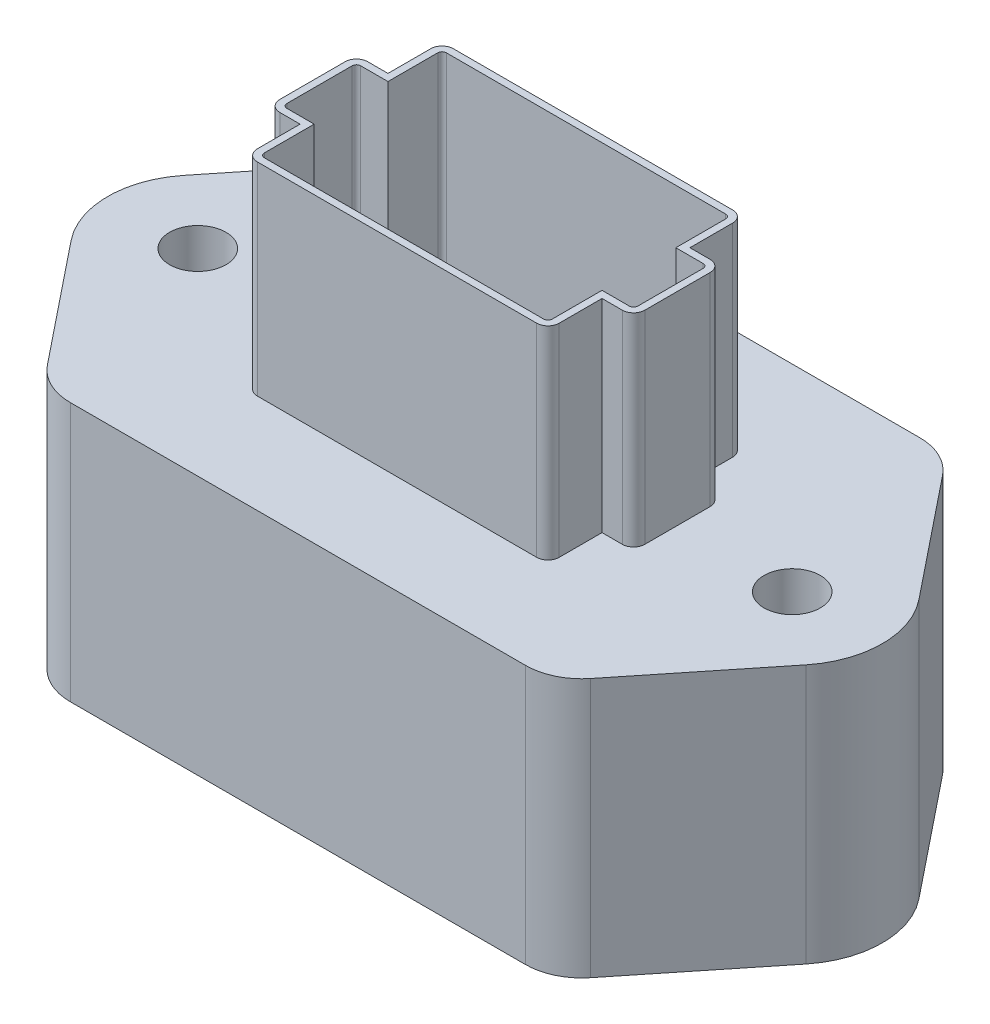
SolidWorks part; units mm, degrees
material "PA Type 6"
ref_plane "Front" through (0, 0, 0) normal (0, 0, 1) x (1, 0, 0)
ref_plane "Top" through (0, 0, 0) normal (0, 1, 0) x (1, 0, 0)
ref_plane "Right" through (0, 0, 0) normal (1, 0, 0) x (0, 0, -1)
sketch "Sketch1" plane through (0, 0, 0) normal (0, 1, 0) x (1, 0, 0)
  line L0 (30.6075, 19.848) -> (41.4283, 6.3568)
  line L1 (-25.654, -22.225) -> (25.654, -22.225)
  line L3 (-25.654, 22.225) -> (25.654, 22.225)
  line L5 (-28.7011, -22.225) -> (28.7011, 22.225) construction
  line L6 (-28.7011, 22.225) -> (28.7011, -22.225) construction
  line L7 (41.4283, -6.3568) -> (30.6075, -19.848)
  line L8 (-30.6075, -19.848) -> (-41.4283, -6.3568)
  line L9 (-41.4283, 6.3568) -> (-30.6075, 19.848)
  line L10 (-28.7011, 22.225) -> (-28.7011, -22.225) construction
  line L11 (28.7011, 22.225) -> (28.7011, -22.225) construction
  arc A0 (25.654, -22.225) -> (30.6075, -19.848) centre (25.654, -15.875) ccw
  arc A1 (-25.654, -22.225) -> (-30.6075, -19.848) centre (-25.654, -15.875) cw
  arc A2 (25.654, 22.225) -> (30.6075, 19.848) centre (25.654, 15.875) cw
  arc A3 (-30.6075, 19.848) -> (-25.654, 22.225) centre (-25.654, 15.875) cw
  arc A4 (41.4283, 6.3568) -> (41.4283, -6.3568) centre (33.5026, 0) cw
  arc A5 (-41.4283, -6.3568) -> (-41.4283, 6.3568) centre (-33.5026, 0) cw
  circle A6 centre (-33.5026, 0) radius 3.175
  circle A7 centre (33.5026, 0) radius 3.175
  point P0 (0, 0)
  dimension "D3" = 6.35
  dimension "D4" = 10.16
  dimension "D6" = 6.35
  dimension "D1" = 44.45
  dimension "D2" = 67.0052
  dimension "D5" = 51.308
extrude "Boss-Extrude1" add sketch "Sketch1" along normal blind 29.21
sketch "Sketch2" plane through (0, 29.21, 0) normal (0, 1, 0) x (1, 0, 0)
  line L0 (0, 11.049) -> (0, -11.049) construction
  line L1 (-15.748, -11.049) -> (15.748, -11.049)
  line L2 (-17.018, -9.779) -> (-17.018, 9.779)
  line L3 (-15.748, 11.049) -> (15.748, 11.049)
  line L4 (17.018, -9.779) -> (17.018, 9.779)
  line L5 (-17.018, -11.049) -> (17.018, 11.049) construction
  line L6 (-17.018, 11.049) -> (17.018, -11.049) construction
  line L7 (17.018, 4.953) -> (19.304, 4.953)
  line L8 (17.018, 4.953) -> (17.018, -4.953)
  line L9 (17.018, -4.953) -> (19.304, -4.953)
  line L10 (20.574, 3.683) -> (20.574, -3.683)
  line L15 (-17.018, -4.953) -> (-19.304, -4.953)
  line L16 (-20.574, 3.683) -> (-20.574, -3.683)
  line L17 (-17.018, 4.953) -> (-19.304, 4.953)
  line L18 (-17.018, 4.953) -> (-17.018, -4.953)
  arc A0 (-20.574, 3.683) -> (-19.304, 4.953) centre (-19.304, 3.683) cw
  arc A1 (-19.304, -4.953) -> (-20.574, -3.683) centre (-19.304, -3.683) cw
  arc A2 (19.304, -4.953) -> (20.574, -3.683) centre (19.304, -3.683) ccw
  arc A3 (19.304, 4.953) -> (20.574, 3.683) centre (19.304, 3.683) cw
  arc A4 (15.748, 11.049) -> (17.018, 9.779) centre (15.748, 9.779) cw
  arc A5 (15.748, -11.049) -> (17.018, -9.779) centre (15.748, -9.779) ccw
  arc A6 (-15.748, -11.049) -> (-17.018, -9.779) centre (-15.748, -9.779) cw
  arc A7 (-17.018, 9.779) -> (-15.748, 11.049) centre (-15.748, 9.779) cw
  point P0 (0, 0)
  point P16 (20.574, 0)
  point P19 (-20.574, 4.953)
  point P22 (-20.574, -4.953)
  point P25 (20.574, -4.953)
  point P28 (20.574, 4.953)
  dimension "D5" = 1.27
  dimension "D1" = 34.036
  dimension "D2" = 22.098
  dimension "D3" = 9.906
  dimension "D4" = 3.556
extrude "Boss-Extrude2" add sketch "Sketch2" along normal blind 22.86 contours A1 L15 L2 L17 A0 L16 | A7 L2 A6 L1 A5 L4 A4 L3 | A3 L7 L4 L9 A2 L10
sketch "Sketch4" plane through (0, 52.07, 0) normal (0, 1, 0) x (1, 0, 0)
  line L0 (-17.018, 4.953) -> (-17.018, 9.779) construction
  line L1 (-17.018, 4.953) -> (-19.304, 4.953) construction
  line L2 (-20.574, 3.683) -> (-20.574, -3.683) construction
  line L3 (-17.018, -4.953) -> (-19.304, -4.953) construction
  line L4 (-17.018, -9.779) -> (-17.018, -4.953) construction
  line L5 (-15.748, -11.049) -> (15.748, -11.049) construction
  line L6 (17.018, -9.779) -> (17.018, -4.953) construction
  line L7 (17.018, -4.953) -> (19.304, -4.953) construction
  line L8 (20.574, 3.683) -> (20.574, -3.683) construction
  line L9 (17.018, 4.953) -> (19.304, 4.953) construction
  line L10 (17.018, 4.953) -> (17.018, 9.779) construction
  line L11 (-15.748, 11.049) -> (15.748, 11.049) construction
  line L12 (-17.018, 4.953) -> (-17.018, 9.779) construction
  line L13 (-17.018, 4.953) -> (-19.304, 4.953) construction
  line L14 (-20.574, 3.683) -> (-20.574, -3.683) construction
  line L15 (-17.018, -4.953) -> (-19.304, -4.953) construction
  line L16 (-17.018, -9.779) -> (-17.018, -4.953) construction
  line L17 (-15.748, -11.049) -> (15.748, -11.049) construction
  line L18 (17.018, -9.779) -> (17.018, -4.953) construction
  line L19 (17.018, -4.953) -> (19.304, -4.953) construction
  line L20 (20.574, 3.683) -> (20.574, -3.683) construction
  line L21 (17.018, 4.953) -> (19.304, 4.953) construction
  line L22 (17.018, 4.953) -> (17.018, 9.779) construction
  line L23 (-15.748, 11.049) -> (15.748, 11.049) construction
  line L24 (-16.2243, 4.1593) -> (-16.2243, 9.779)
  line L25 (-15.748, 10.2553) -> (15.748, 10.2553)
  line L26 (16.2242, 4.1593) -> (16.2242, 9.779)
  line L27 (16.2242, 4.1593) -> (19.304, 4.1593)
  line L28 (19.7803, 3.683) -> (19.7803, -3.683)
  line L29 (16.2242, -4.1592) -> (19.304, -4.1593)
  line L30 (16.2242, -9.779) -> (16.2242, -4.1592)
  line L31 (-15.748, -10.2553) -> (15.748, -10.2553)
  line L32 (-16.2242, -9.779) -> (-16.2243, -4.1592)
  line L33 (-16.2243, -4.1592) -> (-19.304, -4.1592)
  line L34 (-19.7803, 3.683) -> (-19.7803, -3.683)
  line L35 (-16.2243, 4.1593) -> (-19.304, 4.1593)
  arc A0 (-19.304, 4.953) -> (-20.574, 3.683) centre (-19.304, 3.683) ccw construction
  arc A1 (-20.574, -3.683) -> (-19.304, -4.953) centre (-19.304, -3.683) ccw construction
  arc A2 (-17.018, -9.779) -> (-15.748, -11.049) centre (-15.748, -9.779) ccw construction
  arc A3 (15.748, -11.049) -> (17.018, -9.779) centre (15.748, -9.779) ccw construction
  arc A4 (19.304, -4.953) -> (20.574, -3.683) centre (19.304, -3.683) ccw construction
  arc A5 (20.574, 3.683) -> (19.304, 4.953) centre (19.304, 3.683) ccw construction
  arc A6 (17.018, 9.779) -> (15.748, 11.049) centre (15.748, 9.779) ccw construction
  arc A7 (-15.748, 11.049) -> (-17.018, 9.779) centre (-15.748, 9.779) ccw construction
  arc A8 (-19.304, 4.953) -> (-20.574, 3.683) centre (-19.304, 3.683) ccw construction
  arc A9 (-20.574, -3.683) -> (-19.304, -4.953) centre (-19.304, -3.683) ccw construction
  arc A10 (-17.018, -9.779) -> (-15.748, -11.049) centre (-15.748, -9.779) ccw construction
  arc A11 (15.748, -11.049) -> (17.018, -9.779) centre (15.748, -9.779) ccw construction
  arc A12 (19.304, -4.953) -> (20.574, -3.683) centre (19.304, -3.683) ccw construction
  arc A13 (20.574, 3.683) -> (19.304, 4.953) centre (19.304, 3.683) ccw construction
  arc A14 (17.018, 9.779) -> (15.748, 11.049) centre (15.748, 9.779) ccw construction
  arc A15 (-15.748, 11.049) -> (-17.018, 9.779) centre (-15.748, 9.779) ccw construction
  arc A16 (-15.748, 10.2553) -> (-16.2243, 9.779) centre (-15.748, 9.779) ccw
  arc A17 (16.2242, 9.779) -> (15.748, 10.2553) centre (15.748, 9.779) ccw
  arc A18 (19.7803, 3.683) -> (19.304, 4.1593) centre (19.304, 3.683) ccw
  arc A19 (19.304, -4.1593) -> (19.7803, -3.683) centre (19.304, -3.683) ccw
  arc A20 (15.748, -10.2553) -> (16.2242, -9.779) centre (15.748, -9.779) ccw
  arc A21 (-16.2242, -9.779) -> (-15.748, -10.2553) centre (-15.748, -9.779) ccw
  arc A22 (-19.7803, -3.683) -> (-19.304, -4.1592) centre (-19.304, -3.683) ccw
  arc A23 (-19.304, 4.1593) -> (-19.7803, 3.683) centre (-19.304, 3.683) ccw
  dimension "D1" = 0.7937
extrude "Cut-Extrude1" cut sketch "Sketch4" against normal up to next
equation "\"Total Cutting Length\"= \"Cutting Length-Outer\" + \"Cutting Length-Inner\""
equation "\"Amount in ft^2\"= \"Bounding Box Area-Blank\" / 144"
